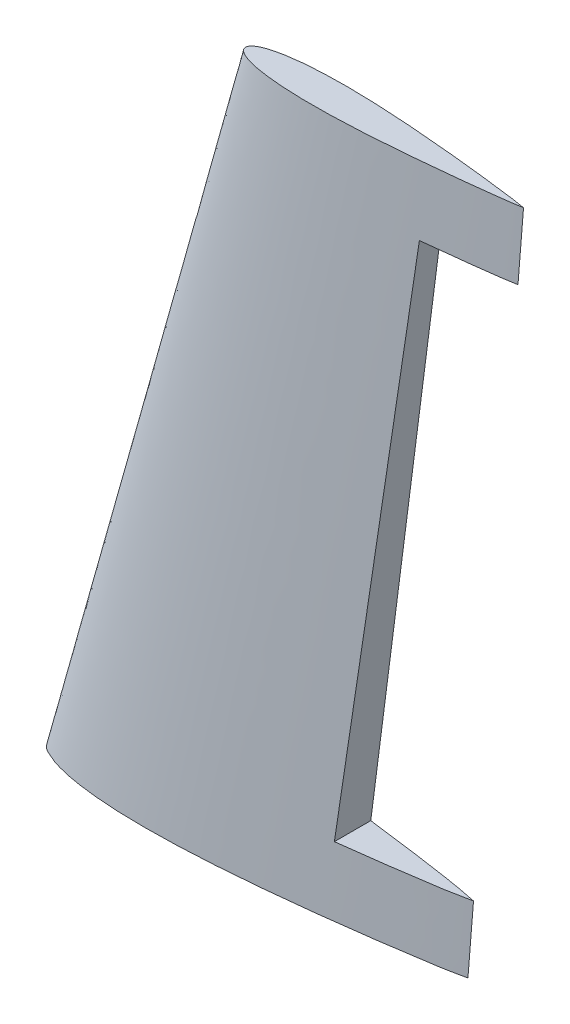
SolidWorks part; units mm, degrees
material "\"PLA\""
ref_plane "Front Plane" through (0, 0, 0) normal (0, 0, 1) x (1, 0, 0)
ref_plane "Top Plane" through (0, 0, 0) normal (0, 1, 0) x (1, 0, 0)
ref_plane "Right Plane" through (0, 0, 0) normal (1, 0, 0) x (0, 0, -1)
sketch "Sketch2" plane through (0, 0, 0) normal (0, 1, 0) x (1, 0, 0)
  line L0 (0, 0) -> (150, 0) construction
  spline S0 degree 3 poles (0, 0) (0.3574, 1.5678) (1.918, 4.1602) (5.9748, 6.0812) (9.6853, 7.4984) (13.5601, 8.4885) (17.359, 9.2744) (21.5371, 9.9268) (26.4618, 10.4957) (33.0301, 11.0042) (39.7779, 11.2375) (48.8818, 11.2764) (58.7619, 11.0016) (68.6835, 10.411) (82.6899, 9.3437) (94.1366, 8.1681) (108.8924, 6.4083) (116.551, 5.4163) (123.9756, 4.3543) (127.9601, 3.7705) (132.3938, 3.1058) (137.1154, 2.4024) (143.0353, 1.4683) (147.2037, 0.5967) (150, 0) knots 0 0 0 0 0.031271 0.055077 0.085653 0.108858 0.132715 0.161158 0.191102 0.229169 0.289323 0.322456 0.406317 0.481621 0.515849 0.679661 0.705503 0.805025 0.829931 0.851453 0.883388 0.917173 0.94435 1 1 1 1
  spline S1 degree 3 poles (0, 0) (0.3941, -1.5488) (1.8634, -4.1083) (5.2872, -5.7362) (8.2332, -6.9993) (11.4396, -7.9611) (14.8376, -8.7747) (18.2267, -9.4129) (21.6079, -9.924) (25.1774, -10.3516) (30.2639, -10.814) (36.5674, -11.1548) (45.6336, -11.3134) (54.66, -11.1386) (65.7291, -10.6179) (80.6284, -9.5535) (94.3915, -8.1361) (108.2354, -6.4878) (115.4814, -5.5561) (124.0381, -4.3507) (129.1858, -3.589) (134.2298, -2.8303) (137.6714, -2.3154) (140.9099, -1.8015) (145.0177, -1.0583) (147.9721, -0.4288) (150, 0) knots 0 0 0 0 0.031459 0.053378 0.072332 0.094059 0.118323 0.140338 0.161138 0.184859 0.210284 0.260514 0.30767 0.386713 0.436157 0.5233 0.677353 0.70536 0.794596 0.819514 0.873511 0.895859 0.918771 0.94123 0.959662 1 1 1 1
  dimension "D1" = 150
ref_plane "Plane1" through (0, 250, 0) normal (0, 1, 0) x (1, 0, 0)
sketch "Sketch3" plane through (0, 250, 0) normal (0, 1, 0) x (1, 0, 0)
  line L0 (70, 0) -> (170, 0) construction
  line L1 (0, 0) -> (150, 0) construction
  spline S2 degree 3 poles (70, 0) (69.9987, 0.5596) (70.4422, 1.2609) (71.2122, 1.8856) (72.1766, 2.5002) (73.3609, 3.0186) (75.1227, 3.6188) (76.6591, 4.0236) (78.4539, 4.4137) (80.7557, 4.834) (83.8645, 5.2529) (87.9614, 5.6338) (93.1248, 5.9241) (99.7601, 6.0454) (107.4686, 5.9211) (115.9679, 5.5565) (125.0641, 4.9667) (134.1697, 4.2123) (143.3561, 3.3275) (150.5367, 2.5503) (156.206, 1.8864) (159.8039, 1.4481) (164.3877, 0.859) (167.7707, 0.4293) (170, 0) knots 0 0 0 0 0.015534 0.023148 0.028948 0.048951 0.06074 0.083424 0.095373 0.114484 0.151868 0.187127 0.23486 0.303157 0.381272 0.460412 0.552057 0.647969 0.727746 0.82209 0.859297 0.894761 0.928143 0.994525 0.994525 0.994525 0.994525
  spline S3 degree 3 poles (70, 0) (69.9987, -0.5596) (70.4422, -1.2609) (71.2122, -1.8856) (72.1766, -2.5002) (73.3609, -3.0186) (75.1227, -3.6188) (76.6591, -4.0236) (78.4539, -4.4137) (80.7557, -4.834) (83.8645, -5.2529) (87.9614, -5.6338) (93.1248, -5.9241) (99.7601, -6.0454) (107.4686, -5.9211) (115.9679, -5.5565) (125.0641, -4.9667) (134.1697, -4.2123) (143.3561, -3.3275) (150.5367, -2.5503) (156.206, -1.8864) (159.8039, -1.4481) (164.3877, -0.859) (167.7707, -0.4293) (170, 0) knots 0 0 0 0 0.015534 0.023148 0.028948 0.048951 0.06074 0.083424 0.095373 0.114484 0.151868 0.187127 0.23486 0.303157 0.381272 0.460412 0.552057 0.647969 0.727746 0.82209 0.859297 0.894761 0.928143 0.994525 0.994525 0.994525 0.994525
  dimension "D1" = 100
  dimension "D2" = 70
loft "Loft1" add profiles "Sketch2", "Sketch3"
sketch "Sketch4" plane through (0, 0, 0) normal (0, 0, 1) x (1, 0, 0)
  line L0 (0, 0) -> (150, 0) construction
  line L1 (150, 0) -> (170, 250) construction
  line L2 (170, 250) -> (70.0002, 250) construction
  line L3 (70.0002, 250) -> (0, 0) construction
  line L4 (150, 0) -> (105, 0) construction
  line L5 (170, 250) -> (140, 250) construction
  line L6 (140, 250) -> (105, 0) construction
  line L7 (140, 250) -> (140, 0) construction
  line L8 (140, 0) -> (140, 25) construction
  line L9 (140, 250) -> (140, 225) construction
  line L10 (152, 25) -> (108.5, 25)
  line L11 (108.5, 25) -> (136.5, 225)
  line L12 (136.5, 225) -> (168, 225)
  line L13 (168, 225) -> (152, 25)
  dimension "D1" = 45
  dimension "D2" = 30
  dimension "D3" = 25
  dimension "D4" = 25
extrude "Cut-Extrude1" cut sketch "Sketch4" against normal through all and the other way through all contours L11 L12 L13 L10
